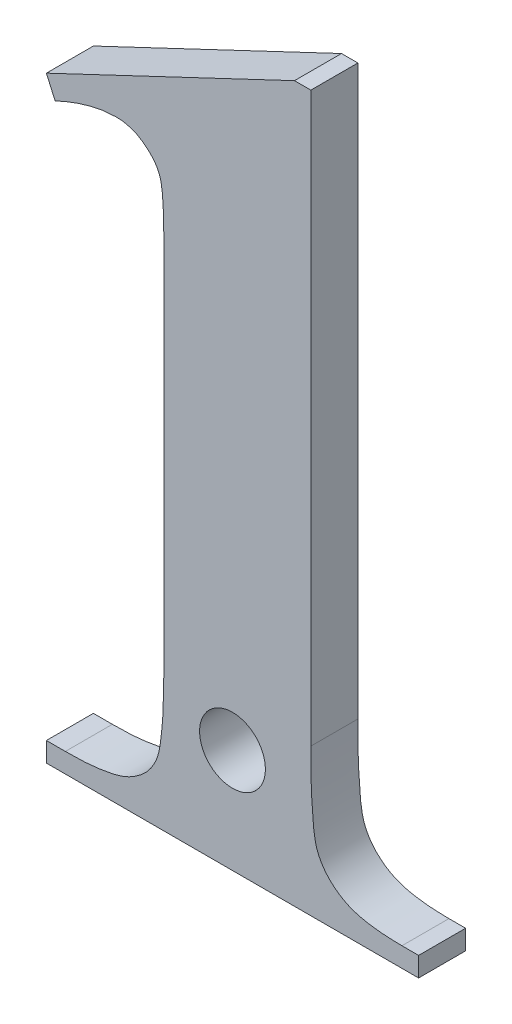
SolidWorks part; units mm, degrees
ref_plane "Plan de face" through (0, 0, 0) normal (0, 0, 1) x (1, 0, 0)
ref_plane "Plan de dessus" through (0, 0, 0) normal (0, 1, 0) x (1, 0, 0)
ref_plane "Plan de droite" through (0, 0, 0) normal (1, 0, 0) x (0, 0, -1)
sketch "Esquisse1" plane through (0, 0, 0) normal (0, 0, 1) x (1, 0, 0)
  text T0 "<b>1</b>" font "Times New Roman" height 30
extrude "Boss.-Extru.1" add sketch "Esquisse1" along normal blind 2
hole_wizard "Dégagement M1.61" positions "Esquisse2" profile "Esquisse3" hole size "M1.6" standard "Ansi Metric"
sketch "Esquisse2" plane through (0, 0, 2) normal (0, 0, 1) x (1, 0, 0)
  point P8 (11.25, 4.431)
sketch "Esquisse3" plane through (11.25, 4.431, 2) normal (1, 0, 0) x (0, -1, 0)
  line L0 (0, 0) -> (0, 50)
  line L1 (0, 50) -> (1.4, 50)
  line L2 (1.4, 50) -> (1.4, 0)
  line L5 (1.4, 0) -> (0, 0)
  line L10 (0, 50) -> (-1.4, 50) construction
  line L11 (0, -6.35) -> (0, 107.95) construction
  dimension "Diamètre du perçage" = 2.8
  dimension "Profondeur du perçage" = 50
  dimension "Angle de pointe" = 180
